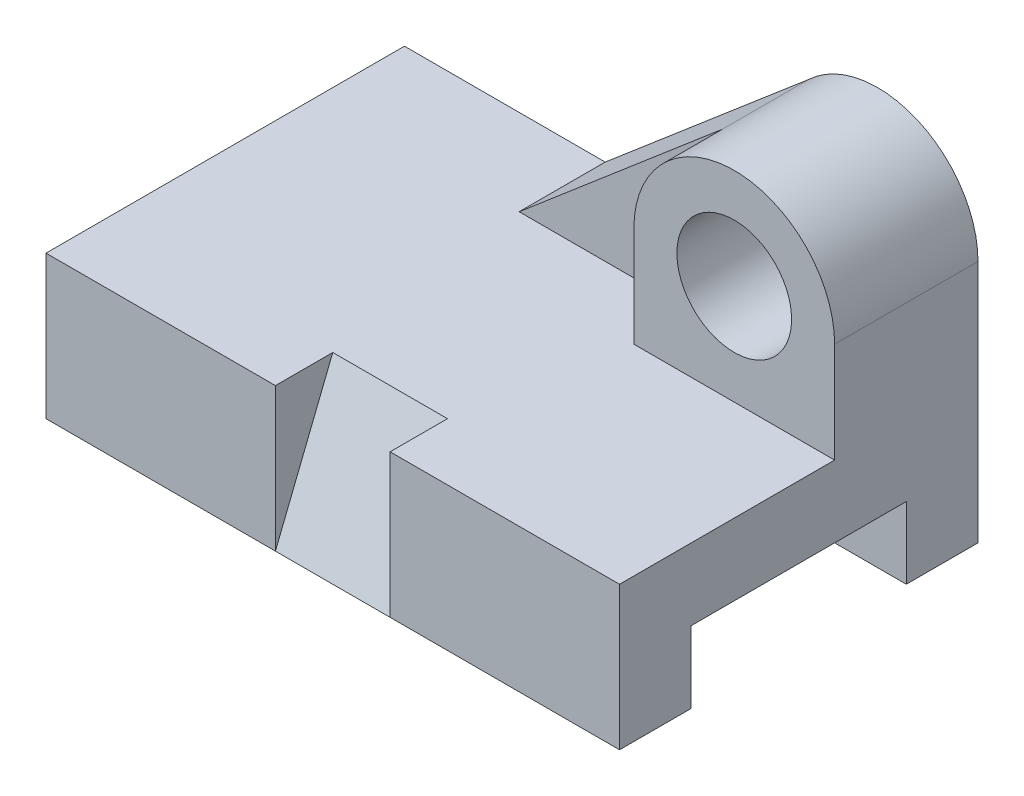
SolidWorks part; units mm, degrees
ref_plane "Front Plane" through (0, 0, 0) normal (0, 0, 1) x (1, 0, 0)
ref_plane "Top Plane" through (0, 0, 0) normal (0, 1, 0) x (1, 0, 0)
ref_plane "Right Plane" through (0, 0, 0) normal (1, 0, 0) x (0, 0, -1)
sketch "Sketch4" plane through (0, 0, 0) normal (0, 1, 0) x (1, 0, 0)
  line L1 (-87.971, 55.0725) -> (112.029, 55.0725)
  line L2 (-87.971, 55.0725) -> (-87.971, -69.9275)
  line L3 (-87.971, -69.9275) -> (112.029, -69.9275)
  line L4 (112.029, 55.0725) -> (112.029, -69.9275)
  dimension "D1" = 200
  dimension "D2" = 125
extrude "Boss-Extrude2" add sketch "Sketch4" along normal blind 50
sketch "Sketch6" plane through (-87.971, 0, 0) normal (-1, 0, 0) x (0, 0, 1)
  line L0 (-55.0725, 0) -> (69.9275, 0) construction
  line L1 (-30.0725, 25) -> (44.9275, 25)
  line L2 (-30.0725, 25) -> (-30.0725, 0)
  line L3 (-30.0725, 0) -> (44.9275, 0)
  line L4 (44.9275, 25) -> (44.9275, 0)
  line L6 (-55.0725, 50) -> (-55.0725, 0) construction
  line L7 (69.9275, 50) -> (69.9275, 0) construction
  dimension "D1" = 75
  dimension "D2" = 25
  dimension "D3" = 25
  dimension "D4" = 25
  dimension "D5" = 35.3553
extrude "Cut-Extrude1" cut sketch "Sketch6" against normal through all
sketch "Sketch7" plane through (0, 0, 69.9275) normal (0, 0, 1) x (1, 0, 0)
  line L0 (-87.971, 50) -> (112.029, 50) construction
  line L1 (-7.971, 50) -> (32.029, 50)
  line L2 (-7.971, 50) -> (-7.971, 0)
  line L3 (-7.971, 0) -> (32.029, 0)
  line L4 (32.029, 50) -> (32.029, 0)
  line L5 (-87.971, 0) -> (112.029, 0) construction
  line L6 (112.029, 50) -> (112.029, 0) construction
  dimension "D1" = 40
  dimension "D2" = 80
extrude "Cut-Extrude2" cut sketch "Sketch7" against normal blind 20
sketch "Sketch9" plane through (32.029, 0, 0) normal (-1, 0, 0) x (0, 0, 1)
  line L0 (49.9275, 50) -> (69.9275, 0)
  line L1 (69.9275, 0) -> (49.9275, 0)
  line L2 (49.9275, 0) -> (49.9275, 50)
extrude "Boss-Extrude5" add sketch "Sketch9" along normal up to surface (40 mm away) up to face at (-7.971, 25, 59.9275)
sketch "Sketch10" plane through (0, 0, -55.0725) normal (0, 0, -1) x (-1, 0, 0)
  line L2 (-42.029, 50) -> (-112.029, 50)
  line L4 (-112.029, 50) -> (-112.029, 85)
  line L5 (-42.029, 85) -> (-42.029, 50)
  line L6 (-112.029, 50) -> (87.971, 50) construction
  arc A1 (-112.029, 85) -> (-42.029, 85) centre (-77.029, 85) cw
  circle A2 centre (-77.029, 85) radius 20
  dimension "D1" = 35
  dimension "D2" = 35
  dimension "D3" = 40
extrude "Boss-Extrude6" add sketch "Sketch10" against normal blind 50
sketch "Sketch11" plane through (0, 0, -55.0725) normal (0, 0, -1) x (-1, 0, 0)
  line L0 (17.971, 50) -> (-55.8357, 112.854)
  line L1 (-42.029, 50) -> (87.971, 50) construction
  line L2 (-42.029, 50) -> (-42.029, 85) construction
  line L3 (-42.029, 50) -> (-42.029, 85)
  line L4 (-42.029, 50) -> (17.971, 50)
  arc A0 (-42.029, 85) -> (-112.029, 85) centre (-77.029, 85) ccw construction
  arc A1 (-42.029, 85) -> (-55.8357, 112.854) centre (-77.029, 85) ccw
  line M4 (87.971, 50) -> (-42.029, 50)
  line M5 (-42.029, 50) -> (-42.029, 85)
  arc M6 (-42.029, 85) -> (-112.029, 85) centre (-77.029, 85) ccw
  dimension "D1" = 70
extrude "Boss-Extrude8" add sketch "Sketch11" against normal blind 30 contours L0 M4 M6 M5
